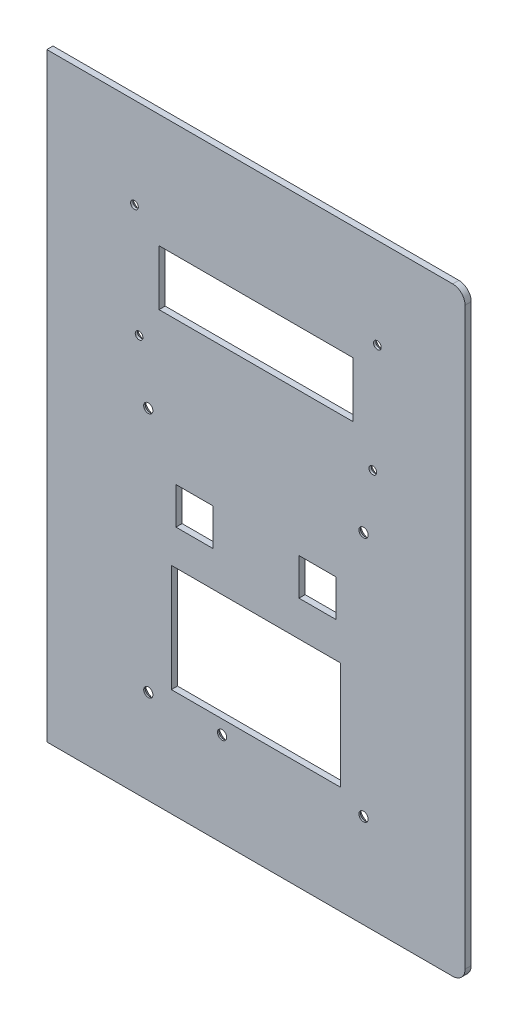
SolidWorks part; units mm, degrees
ref_plane "Plan de face" through (0, 0, 0) normal (0, 0, 1) x (1, 0, 0)
ref_plane "Plan de dessus" through (0, 0, 0) normal (0, 1, 0) x (1, 0, 0)
ref_plane "Plan de droite" through (0, 0, 0) normal (1, 0, 0) x (0, 0, -1)
sketch "Esquisse1" plane through (0, 0, 0) normal (0, 0, 1) x (1, 0, 0)
  line L1 (0, 0) -> (-136, 0)
  line L2 (0, 0) -> (0, 195)
  line L3 (0, 195) -> (-136, 195)
  line L4 (-136, 0) -> (-136, 195)
  line L5 (-107.5, 165.5) -> (-28.5, 165.5) construction
  line L7 (-106, 129.5) -> (-30, 129.5) construction
  line L9 (-99.5, 158) -> (-36.5, 158)
  line L10 (-99.5, 158) -> (-99.5, 140)
  line L11 (-99.5, 140) -> (-36.5, 140)
  line L12 (-36.5, 158) -> (-36.5, 140)
  line L13 (-103, 110.5) -> (-33, 110.5) construction
  line L14 (-103, 110.5) -> (-103, 30.5) construction
  line L15 (-103, 30.5) -> (-33, 30.5) construction
  line L16 (-33, 110.5) -> (-33, 30.5) construction
  line L17 (-94, 93.5) -> (-82, 93.5)
  line L18 (-94, 93.5) -> (-94, 81.5)
  line L19 (-94, 81.5) -> (-82, 81.5)
  line L20 (-82, 93.5) -> (-82, 81.5)
  line L21 (-54, 93.5) -> (-42, 93.5)
  line L22 (-54, 93.5) -> (-54, 81.5)
  line L23 (-54, 81.5) -> (-42, 81.5)
  line L24 (-42, 93.5) -> (-42, 81.5)
  line L25 (-95.5, 70) -> (-40.5, 70)
  line L26 (-95.5, 70) -> (-95.5, 35)
  line L27 (-95.5, 35) -> (-40.5, 35)
  line L28 (-40.5, 70) -> (-40.5, 35)
  circle A0 centre (-107.5, 165.5) radius 1.25
  circle A1 centre (-28.5, 165.5) radius 1.25
  circle A2 centre (-30, 129.5) radius 1.25
  circle A3 centre (-106, 129.5) radius 1.25
  circle A4 centre (-103, 110.5) radius 1.5
  circle A5 centre (-33, 110.5) radius 1.5
  circle A6 centre (-33, 30.5) radius 1.5
  circle A7 centre (-103, 30.5) radius 1.5
  circle A8 centre (-79, 30.5) radius 1.5
  dimension "D25" = 2.5
  dimension "D26" = 3
  dimension "D1" = 136
  dimension "D2" = 195
  dimension "D3" = 140
  dimension "D4" = 63
  dimension "D5" = 18
  dimension "D6" = 36.5
  dimension "D7" = 28.5
  dimension "D8" = 33
  dimension "D9" = 30.5
  dimension "D10" = 110.5
  dimension "D11" = 103
  dimension "D12" = 42
  dimension "D13" = 82
  dimension "D14" = 81.5
  dimension "D15" = 12
  dimension "D16" = 55
  dimension "D17" = 35
  dimension "D18" = 40.5
  dimension "D19" = 35
  dimension "D20" = 30
  dimension "D21" = 106
  dimension "D22" = 107.5
  dimension "D23" = 165.5
  dimension "D24" = 129.5
  dimension "D27" = 57
extrude "Extrusion1" add sketch "Esquisse1" along normal mid plane 2
chamfer "Chanfrein1" distance 1.5 angle 45 5 edges at (-101.5, 110.5, -1) (-31.5, 110.5, -1) (-31.5, 30.5, -1) (-101.5, 30.5, -1) (-77.5, 30.5, -1)
fillet "Congé1" radius 4 2 edges at (0, 0, 0) (0, 195, 0)
chamfer "Chanfrein2" distance 1.25 angle 45 4 edges at (-106.25, 165.5, -1) (-27.25, 165.5, -1) (-28.75, 129.5, -1) (-104.75, 129.5, -1)
